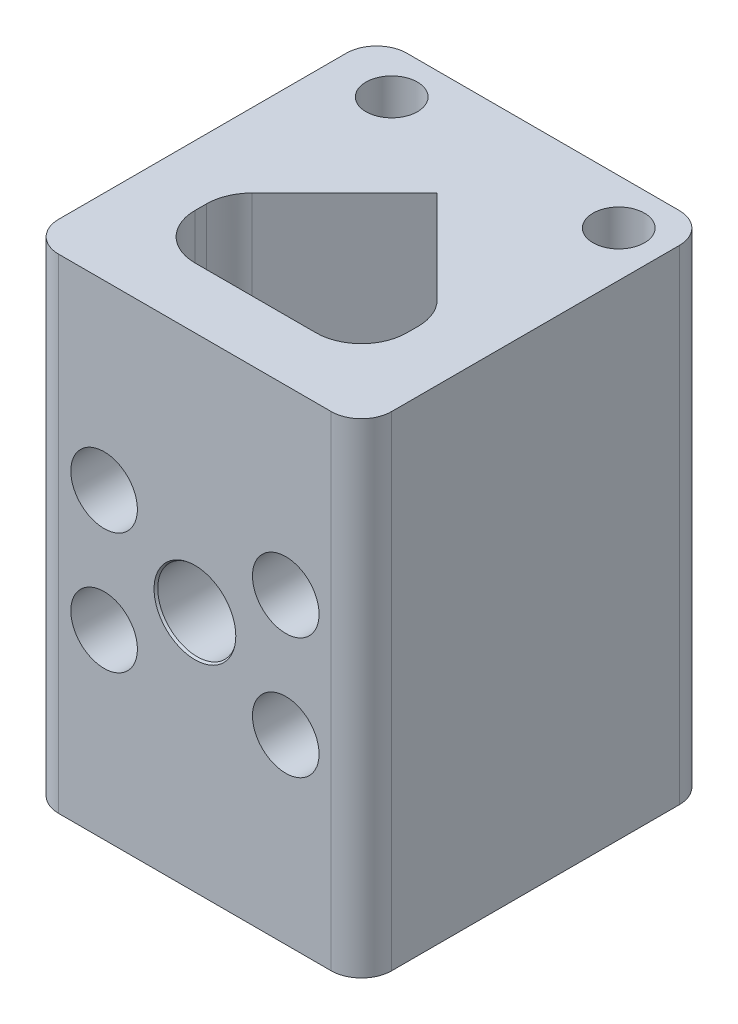
SolidWorks part; units mm, degrees
ref_plane "Front Plane" through (0, 0, 0) normal (0, 0, 1) x (1, 0, 0)
ref_plane "Top Plane" through (0, 0, 0) normal (0, 1, 0) x (1, 0, 0)
ref_plane "Right Plane" through (0, 0, 0) normal (1, 0, 0) x (0, 0, -1)
sketch "Sketch1" plane through (0, 0, 0) normal (0, 1, 0) x (1, 0, 0)
  line L1 (0, 0) -> (22, 0)
  line L2 (0, 0) -> (0, 23)
  line L3 (0, 23) -> (22, 23)
  line L4 (22, 0) -> (22, 23)
  line L14 (4, 4) -> (18, 4)
  line L20 (11, 23) -> (11, 0) construction
  line L21 (4, 19) -> (18, 19) construction
  line L22 (4, 4) -> (4, 19) construction
  line L23 (18, 4) -> (18, 19) construction
  line L24 (4, 4) -> (4, 9)
  line L25 (4, 9) -> (11, 16)
  line L26 (11, 16) -> (18, 9)
  line L27 (18, 9) -> (18, 4)
  dimension "D1" = 23
  dimension "D2" = 22
  dimension "D4" = 90
  dimension "D5" = 5
  dimension "D3" = 4
extrude "Boss-Extrude1" add sketch "Sketch1" along normal blind 32
fillet "Fillet1" radius 3 4 edges at (18, 16, -4) (4, 16, -4) (4, 16, -9) (18, 16, -9)
hole_wizard "CBORE for M2 SHCS1" positions "Sketch4" profile "Sketch6" counterbore size "M2" standard "ANSI Metric" end condition through all
sketch "Sketch4" plane through (0, 0, 0) normal (0, 0, 1) x (1, 0, 0)
  line L0 (0, 0) -> (22, 0) construction
  line L1 (0, 32) -> (0, 0) construction
  point P0 (5, 12)
  point P12 (17, 12)
  point P13 (17, 20)
  point P14 (5, 20)
  dimension "D1" = 12
  dimension "D2" = 5
  dimension "D3" = 2
  dimension "D4" = 2
sketch "Sketch6" plane through (5, 12, 0) normal (1, 0, 0) x (0, -1, 0)
  line L0 (0, 0) -> (0, 23)
  line L1 (0, 23) -> (1.2, 23)
  line L3 (1.2, 23) -> (1.2, 21)
  line L4 (1.2, 21) -> (2.2, 21)
  line L5 (2.2, 21) -> (2.2, 0)
  line L7 (2.2, 0) -> (0, 0)
  line L11 (0, -6.35) -> (0, 107.95) construction
  dimension "Thru Hole Dia." = 2.4
  dimension "Thru Hole Depth" = 23
  dimension "C'Bore Dia." = 4.4
  dimension "C'Bore Depth" = 21
hole_wizard "Ø5.0mm Dowel Hole1" positions "Sketch7" profile "Sketch8" hole size "Ø5.0" standard "ANSI Metric" end condition up to next
sketch "Sketch7" plane through (0, 0, 0) normal (0, 0, 1) x (1, 0, 0)
  line L0 (0, 32) -> (0, 0) construction
  line L1 (0, 0) -> (22, 0) construction
  point P0 (11, 16)
  point P5 (0, 16)
  dimension "D1" = 11
  dimension "D2" = 16
sketch "Sketch8" plane through (11, 16, 0) normal (1, 0, 0) x (0, -1, 0)
  line L0 (0, 0) -> (0, 4)
  line L1 (0, 4) -> (2.6, 4)
  line L2 (2.6, 4) -> (2.6, 0.1428)
  line L3 (2.6, 0.1428) -> (2.7, 0)
  line L5 (2.7, 0) -> (0, 0)
  line L6 (-2.6, 0.1428) -> (-2.7, 0) construction
  line L11 (0, -6.35) -> (0, 107.95) construction
  dimension "Thru Hole Dia." = 5.2
  dimension "Thru Hole Depth" = 4
  dimension "Near C'Sink Dia." = 5.4
  dimension "Near C'Sink Angle" = 70
fillet "Fillet2" radius 2 4 edges at (22, 16, -23) (0, 16, -23) (22, 16, 0) (0, 16, 0)
hole_wizard "M3 Clearance Hole1" positions "Sketch9" profile "Sketch10" hole size "M3" standard "ANSI Metric"
sketch "Sketch9" plane through (0, 32, 0) normal (0, 1, 0) x (1, 0, 0)
  line L1 (2, 23) -> (20, 23) construction
  line L3 (22, 2) -> (22, 21) construction
  point P0 (4, 20)
  point P2 (19, 20)
  dimension "D1" = 15
  dimension "D2" = 3
  dimension "D3" = 3
  dimension "D4" = 3
sketch "Sketch10" plane through (4, 32, -20) normal (1, 0, 0) x (0, 0, 1)
  line L0 (0, 0) -> (0, 8.5215)
  line L1 (0, 8.5215) -> (1.7, 7.5)
  line L2 (1.7, 7.5) -> (1.7, 0)
  line L5 (1.7, 0) -> (0, 0)
  line L10 (0, 8.5215) -> (-1.7, 7.5) construction
  line L11 (0, -6.35) -> (0, 107.95) construction
  dimension "Hole Dia." = 3.4
  dimension "Hole Depth" = 7.5
  dimension "Drill Angle" = 118
